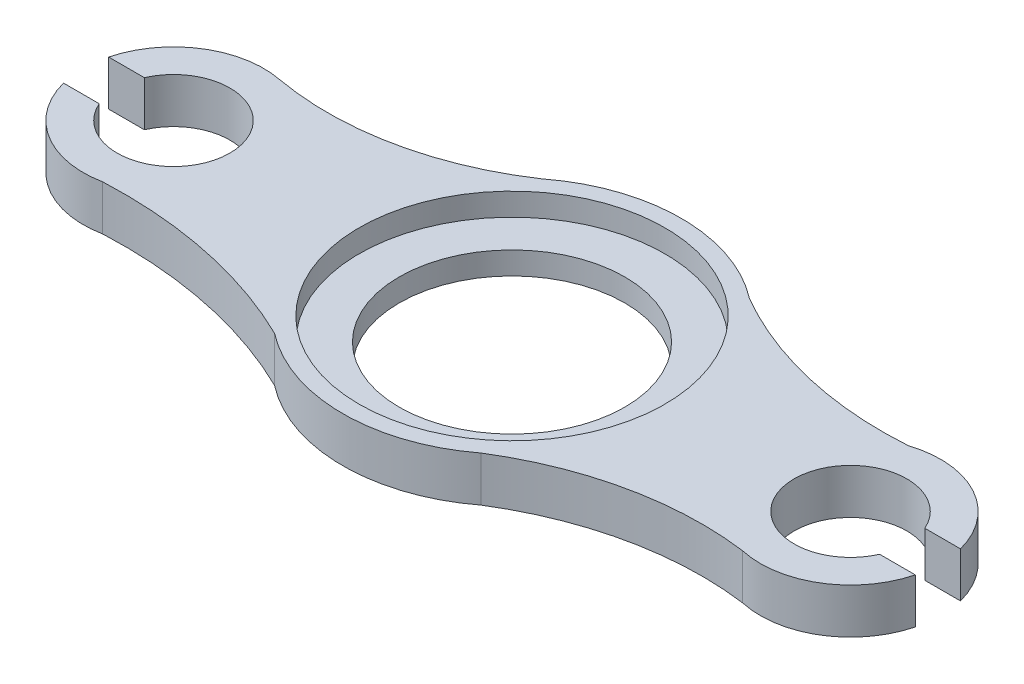
SolidWorks part; units mm, degrees
material "AISI 1020"
ref_plane "Plan de face" through (0, 0, 0) normal (0, 0, 1) x (1, 0, 0)
ref_plane "Plan de dessus" through (0, 0, 0) normal (0, 1, 0) x (1, 0, 0)
ref_plane "Plan de droite" through (0, 0, 0) normal (1, 0, 0) x (0, 0, -1)
sketch "Esquisse1" plane through (0, 0, 0) normal (0, 1, 0) x (1, 0, 0)
  line L1 (-190, 75) -> (190, 75)
  line L2 (-190, 75) -> (-190, -75)
  line L3 (-190, -75) -> (190, -75)
  line L4 (190, 75) -> (190, -75)
extrude "Boss.-Extru.1" add sketch "Esquisse1" along normal blind 20
sketch "Esquisse2" plane through (0, 0, 0) normal (0, -1, 0) x (-1, 0, 0)
  line L3 (200.0174, -10) -> (159.2556, -10)
  line L4 (200.0174, -10) -> (200.0174, 10)
  line L5 (200.0174, 10) -> (159.2556, 10)
  line L6 (159.2556, -10) -> (159.2556, 10)
  line L7 (-154.9898, -10) -> (-226.086, -10)
  line L8 (-154.9898, -10) -> (-154.9898, 10)
  line L9 (-154.9898, 10) -> (-226.086, 10)
  line L10 (-226.086, -10) -> (-226.086, 10)
  circle A0 centre (0, 0) radius 50
  circle A1 centre (0, 0) radius 67.75
  circle A2 centre (150, 0) radius 25
  circle A3 centre (-150, 0) radius 25
  line M11 (190, -75) -> (190, 75)
  line M13 (-190, 75) -> (-190, -75)
extrude "Enlèv. mat.-Extru.2" cut sketch "Esquisse2" against normal through all contours A2 L3 L5 M11 | L5 A2 L3 L6 | L3 A2 L5 L6 | A0 | L7 A3 L9 L8 | L9 A3 L7 L8 | L10 L7 L9 M13 | A3 L9 L7 M13
sketch "Esquisse4" plane through (0, 20, 0) normal (0, 1, 0) x (1, 0, 0)
  circle A0 centre (0, 0) radius 67.75
extrude "Enlèv. mat.-Extru.3" cut sketch "Esquisse4" against normal blind 10 contours A0
sketch "Esquisse5" plane through (0, 20, 0) normal (0, 1, 0) x (1, 0, 0)
  circle A0 centre (-150, 0) radius 40
  circle A1 centre (150, 0) radius 40
  circle A2 centre (0, 0) radius 75
  arc A3 (-45.987, 59.2469) -> (-142.1925, 39.2306) centre (-118.8107, 168.0569) cw
  arc A4 (45.987, 59.2469) -> (137.6837, 38.0566) centre (126.3472, 197.995) ccw
  arc A5 (-142.1925, -39.2306) -> (-45.987, -59.2469) centre (-133.0554, -236.5218) cw
  arc A6 (141.1237, -39.0027) -> (45.6719, -59.4902) centre (121.9108, -182.0894) ccw
  line M6 (-190, 10) -> (-172.9129, 10)
  line M8 (-172.9129, -10) -> (-190, -10)
  line M9 (-190, -10) -> (-190, -75)
  line M10 (-190, -75) -> (190, -75)
  line M11 (190, -75) -> (190, -10)
  line M12 (190, -10) -> (172.9129, -10)
  line M14 (172.9129, 10) -> (190, 10)
  line M15 (190, 10) -> (190, 75)
  line M16 (190, 75) -> (-190, 75)
  line M17 (-190, 75) -> (-190, 10)
extrude "Enlèv. mat.-Extru.4" cut sketch "Esquisse5" against normal through all contours A5 A0 A2 M8 M9 M10 | A3 A2 A0 M16 M17 M6 | A2 A4 A1 M14 M15 M16 | A1 A6 A2 M10 M11 M12
